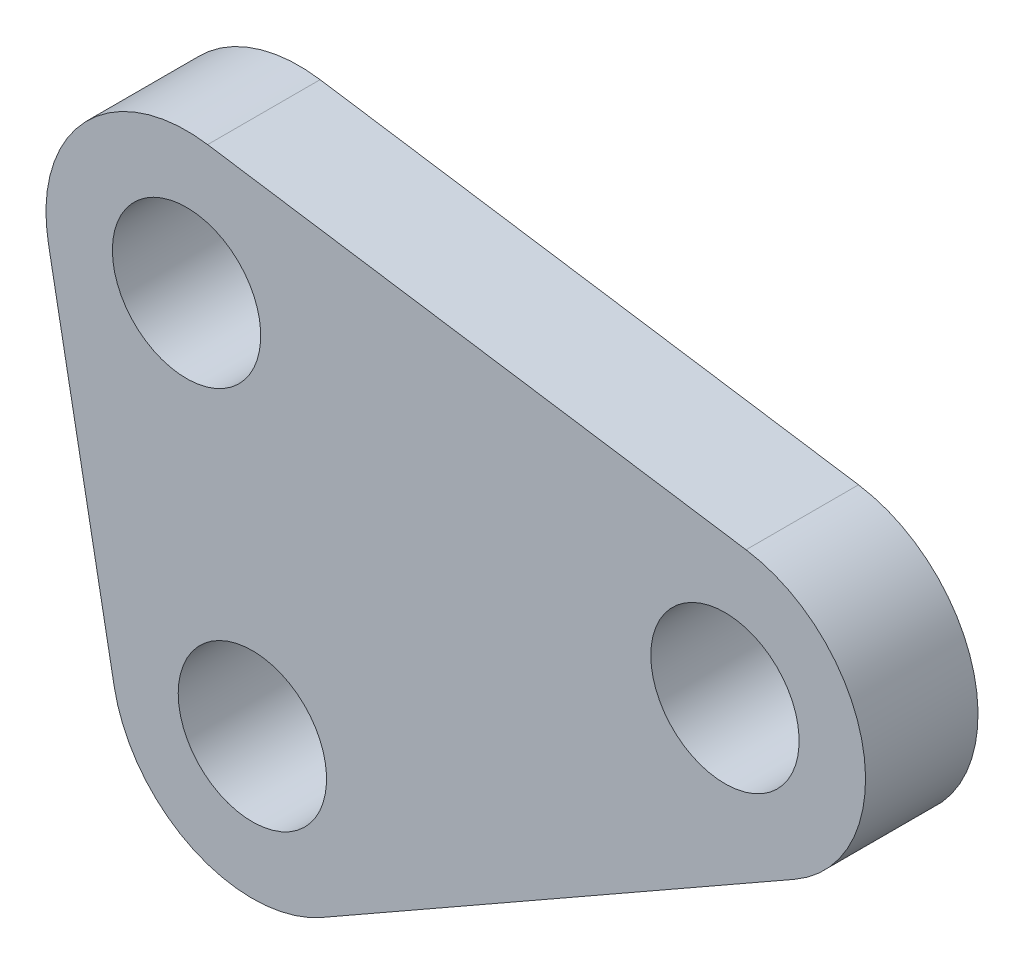
SolidWorks part; units mm, degrees
material "PLA"
ref_plane "Front Plane" through (0, 0, 0) normal (0, 0, 1) x (1, 0, 0)
ref_plane "Top Plane" through (0, 0, 0) normal (0, 1, 0) x (1, 0, 0)
ref_plane "Right Plane" through (0, 0, 0) normal (1, 0, 0) x (0, 0, -1)
ref_plane "Plane1" through (0, 0, 4) normal (0, 0, 1) x (1, 0, 0)
sketch "Sketch1" plane through (0, 0, 4) normal (0, 0, 1) x (1, 0, 0)
  line L0 (46.038, 74.1382) -> (26.8916, 77.0426)
  line L1 (21.2274, 71.1774) -> (23.5682, 58.6966)
  line L2 (30.958, 55.2742) -> (47.7636, 64.8506)
  circle A0 centre (45.2881, 69.1948) radius 2.6375
  circle A1 centre (26.1417, 72.0991) radius 2.6375
  arc A2 (47.7636, 64.8506) -> (46.038, 74.1382) centre (45.2881, 69.1948) ccw
  arc A3 (26.8916, 77.0426) -> (21.2274, 71.1774) centre (26.1417, 72.0991) ccw
  arc A4 (23.5682, 58.6966) -> (30.958, 55.2742) centre (28.4826, 59.6183) ccw
  circle A5 centre (28.4826, 59.6183) radius 2.6375
extrude "Boss-Extrude1" add sketch "Sketch1" against normal blind 4
